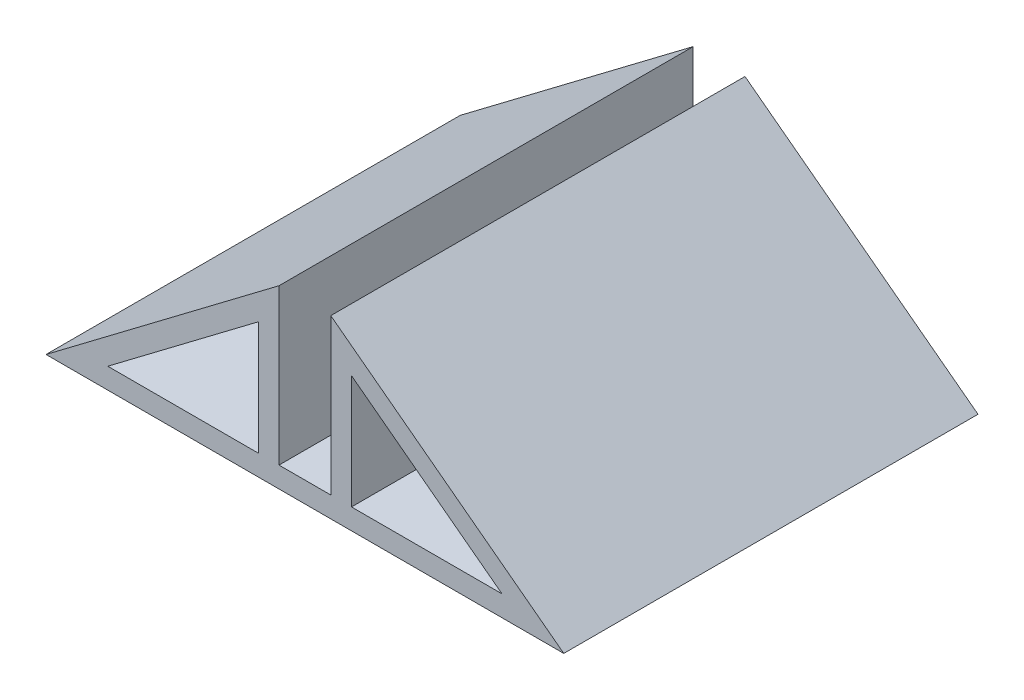
SolidWorks part; units mm, degrees
ref_plane "Plan de face" through (0, 0, 0) normal (0, 0, 1) x (1, 0, 0)
ref_plane "Plan de dessus" through (0, 0, 0) normal (0, 1, 0) x (1, 0, 0)
ref_plane "Plan de droite" through (0, 0, 0) normal (1, 0, 0) x (0, 0, -1)
sketch "Esquisse1" plane through (0, 0, 0) normal (0, 0, 1) x (1, 0, 0)
  line L0 (-132.2869, -48.9325) -> (-182.2869, -48.9325)
  line L1 (-182.2869, -48.9325) -> (-159.7869, -31.9325)
  line L2 (-132.2869, -48.9325) -> (-154.7869, -31.9325)
  line L3 (-157.2869, -8.1475) -> (-157.2869, -37.9275) construction
  line L4 (-159.7869, -31.9325) -> (-159.7869, -46.9325)
  line L5 (-154.7869, -46.9325) -> (-159.7869, -46.9325)
  line L6 (-154.7869, -46.9325) -> (-159.7869, -46.9325)
  line L7 (-154.7869, -31.9325) -> (-154.7869, -46.9325)
  line L8 (-152.7869, -35.9503) -> (-152.7869, -46.9325)
  line L9 (-152.7869, -46.9325) -> (-138.2516, -46.9325)
  line L10 (-138.2516, -46.9325) -> (-152.7869, -35.9503)
  line L11 (-176.3222, -46.9325) -> (-161.7869, -35.9503)
  line L12 (-161.7869, -46.9325) -> (-176.3222, -46.9325)
  line L13 (-161.7869, -35.9503) -> (-161.7869, -46.9325)
  point P4 (-151.6724, -47.3812)
  point P8 (-157.2869, -48.9325)
  point P10 (-157.2869, -46.9325)
  point P12 (-151.6504, -46.9325)
  point P18 (0, 0)
  point P19 (0, 0)
  dimension "D1" = 5
  dimension "D2" = 2
  dimension "D3" = 50
  dimension "D4" = 15
  dimension "D5" = 2
  dimension "D6" = 2
  dimension "D7" = 2
extrude "Boss.-Extru.2" add sketch "Esquisse1" along normal blind 40 contours L2 L7 L5 L4 L1 L0 L10 L9 L8 L11 L13 L12
